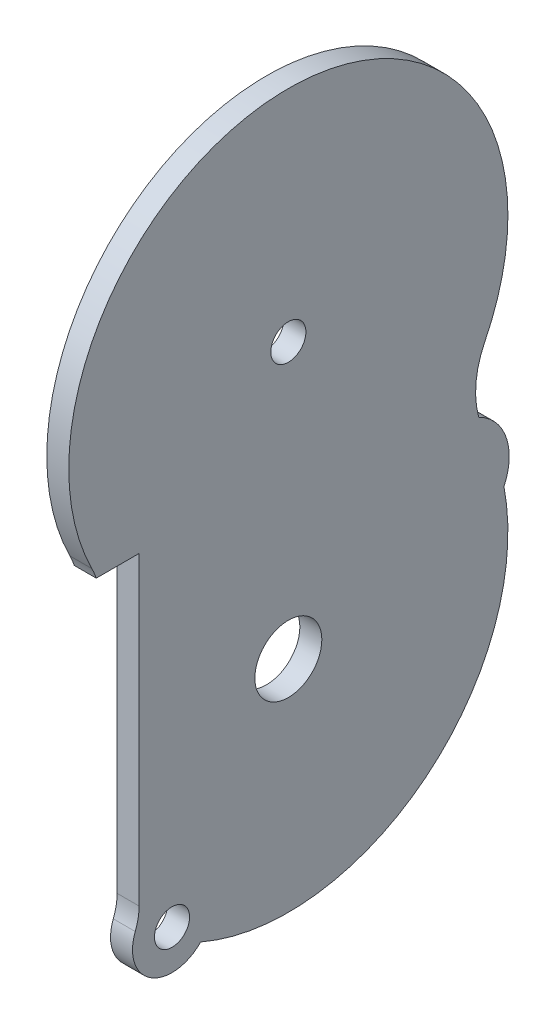
SolidWorks part; units mm, degrees
ref_plane "Front Plane" through (0, 0, 0) normal (0, 0, 1) x (1, 0, 0)
ref_plane "Top Plane" through (0, 0, 0) normal (0, 1, 0) x (1, 0, 0)
ref_plane "Right Plane" through (0, 0, 0) normal (1, 0, 0) x (0, 0, -1)
sketch "Sketch1" plane through (-4.9338, 0, 0) normal (1, 0, 0) x (0, 0, -1)
  line L0 (6.5085, -3.583) -> (8.3164, -3.583)
  line L1 (8.3164, -3.583) -> (8.3164, -30.4953)
  line L4 (8.3164, -30.4953) -> (8.3164, -31.395)
  line L5 (4.417, -3.583) -> (6.5085, -3.583)
  line L8 (4.417, -3.583) -> (6.5085, -3.583)
  line L14 (8.3164, -31.395) -> (8.3164, -30.4953)
  arc A0 (12.7244, -35.3109) -> (10.0757, -33.5407) centre (11.3164, -34.5509) ccw construction
  circle A1 centre (21.9114, 6.302) radius 1.6 construction
  arc A2 (12.7244, -35.3109) -> (10.0757, -33.5407) centre (11.3164, -34.5509) ccw
  circle A3 centre (21.9114, 6.302) radius 1.6
  circle A4 centre (21.9114, -18.698) radius 3.05
  arc A5 (20.1655, -20.5566) -> (23.6655, -20.5489) centre (21.9114, -18.698) ccw construction
  arc A15 (14.0416, -34.8865) -> (39.5673, -15.1953) centre (21.9114, -18.698) ccw
  arc A16 (14.0416, -34.8865) -> (12.7244, -35.3109) centre (13.6044, -35.7858) ccw
  arc A17 (10.0757, -33.5407) -> (12.7244, -35.3109) centre (11.3164, -34.5509) ccw
  arc A18 (10.0757, -33.5407) -> (9.964, -32.1613) centre (9.3003, -32.9092) ccw
  arc A19 (8.3164, -30.4953) -> (9.964, -32.1613) centre (21.9114, -18.698) ccw
  arc A20 (7.9676, -33.2298) -> (13.9234, -37.0336) centre (11.3164, -34.5509) ccw
  arc A21 (13.9234, -37.0336) -> (41.5515, -14.9206) centre (21.9114, -18.698) ccw
  arc A22 (41.5515, -14.9206) -> (39.2477, -8.301) centre (37.0314, -12.783) ccw
  arc A23 (39.8078, -2.6266) -> (39.2477, -8.301) centre (46.9664, -6.198) ccw
  arc A24 (39.8078, -2.6266) -> (4.015, -2.6266) centre (21.9114, 6.302) ccw
  arc A25 (4.417, -3.583) -> (4.015, -2.6266) centre (-3.1435, -6.198) ccw
  arc A26 (6.5085, -3.583) -> (5.8047, -1.7337) centre (-3.1435, -6.198) ccw
  arc A27 (38.0182, -1.7337) -> (5.8047, -1.7337) centre (21.9114, 6.302) ccw
  arc A28 (38.0182, -1.7337) -> (37.4628, -9.3097) centre (46.9664, -6.198) ccw
  arc A29 (39.5673, -15.1953) -> (37.4628, -9.3097) centre (37.0314, -12.783) ccw
  arc A30 (14.0416, -34.8865) -> (39.5673, -15.1953) centre (21.9114, -18.698) ccw
  arc A31 (14.0416, -34.8865) -> (12.7244, -35.3109) centre (13.6044, -35.7858) ccw
  arc A32 (10.0757, -33.5407) -> (12.7244, -35.3109) centre (11.3164, -34.5509) ccw
  arc A33 (10.0757, -33.5407) -> (9.964, -32.1613) centre (9.3003, -32.9092) ccw
  arc A34 (8.3164, -30.4953) -> (9.964, -32.1613) centre (21.9114, -18.698) ccw
  arc A35 (7.9676, -33.2298) -> (13.9234, -37.0336) centre (11.3164, -34.5509) ccw
  arc A36 (13.9234, -37.0336) -> (41.5515, -14.9206) centre (21.9114, -18.698) ccw
  arc A37 (41.5515, -14.9206) -> (39.2477, -8.301) centre (37.0314, -12.783) ccw
  arc A38 (39.8078, -2.6266) -> (39.2477, -8.301) centre (46.9664, -6.198) ccw
  arc A39 (39.8078, -2.6266) -> (4.015, -2.6266) centre (21.9114, 6.302) ccw
  arc A40 (4.417, -3.583) -> (4.015, -2.6266) centre (-3.1435, -6.198) ccw
  arc A41 (6.5085, -3.583) -> (5.8047, -1.7337) centre (-3.1435, -6.198) ccw
  arc A42 (38.0182, -1.7337) -> (5.8047, -1.7337) centre (21.9114, 6.302) ccw
  arc A43 (38.0182, -1.7337) -> (37.4628, -9.3097) centre (46.9664, -6.198) ccw
  arc A44 (39.5673, -15.1953) -> (37.4628, -9.3097) centre (37.0314, -12.783) ccw
  arc A66 (7.9676, -33.2298) -> (8.3164, -31.395) centre (3.3164, -31.395) ccw construction
  arc A67 (7.9676, -33.2298) -> (8.3164, -31.395) centre (3.3164, -31.395) ccw
  arc A84 (7.9676, -33.2298) -> (8.3164, -31.395) centre (3.3164, -31.395) ccw
  arc A85 (7.9676, -33.2298) -> (8.3164, -31.395) centre (3.3164, -31.395) ccw
  dimension "D2" = 0.5
  dimension "D1" = 0
extrude "Boss-Extrude1" add sketch "Sketch1" along normal blind 2
